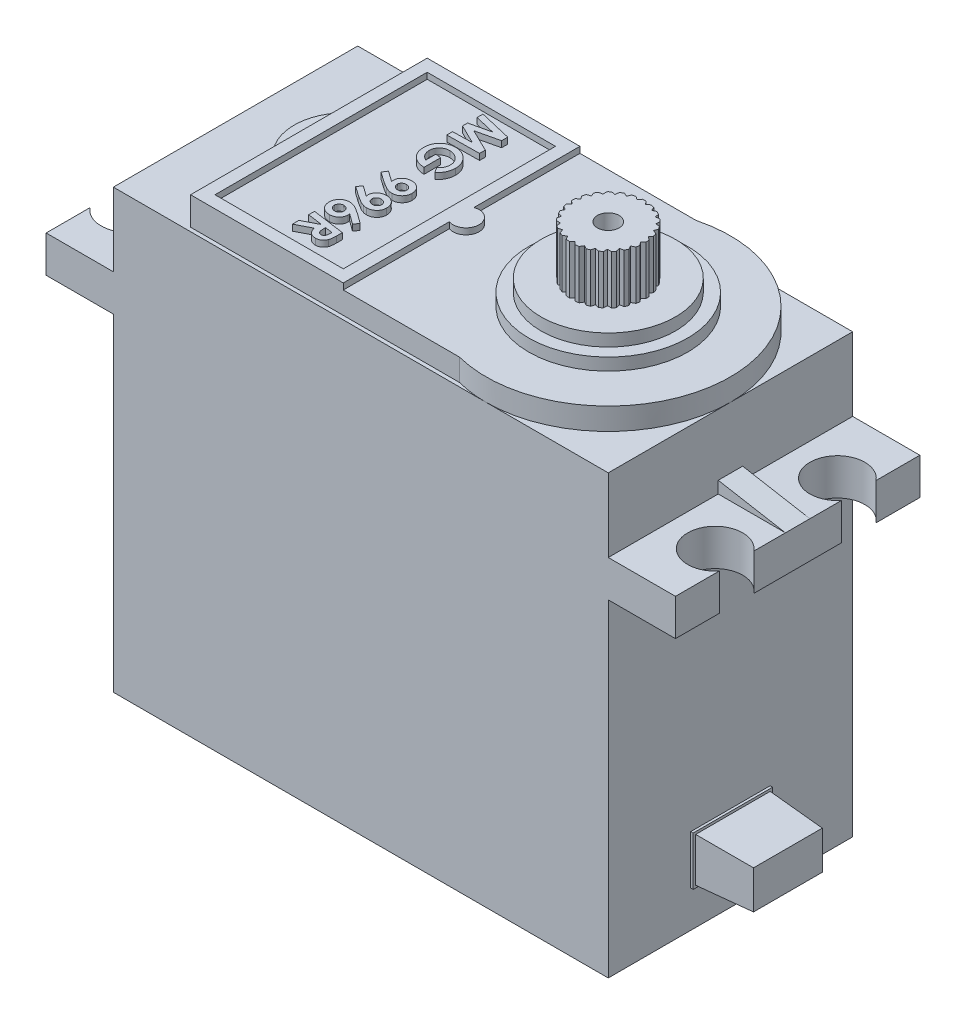
SolidWorks part; units mm, degrees
ref_plane "Plan de face" through (0, 0, 0) normal (0, 0, 1) x (1, 0, 0)
ref_plane "Plan de dessus" through (0, 0, 0) normal (0, 1, 0) x (1, 0, 0)
ref_plane "Plan de droite" through (0, 0, 0) normal (1, 0, 0) x (0, 0, -1)
sketch "Esquisse2" plane through (0, 0, 0) normal (0, 1, 0) x (1, 0, 0)
  line L1 (0, 0) -> (40.5, 0)
  line L2 (0, 0) -> (0, 20)
  line L3 (0, 20) -> (40.5, 20)
  line L4 (40.5, 0) -> (40.5, 20)
  dimension "D1" = 20
  dimension "D2" = 40.5
extrude "Boss.-Extru.1" add sketch "Esquisse2" along normal blind 36.8
chamfer "Chanfrein1" distance 1 angle 45 4 edges at (20.25, 0, 0) (40.5, 0, -10) (20.25, 0, -20) (0, 0, -10)
sketch "Esquisse3" plane through (40.5, 0, 0) normal (1, 0, 0) x (0, 0, -1)
  line L0 (19, 0) -> (1, 0) construction
  line L1 (6.75, 8) -> (13.25, 8)
  line L2 (6.75, 8) -> (6.75, 4)
  line L3 (6.75, 4) -> (13.25, 4)
  line L4 (13.25, 8) -> (13.25, 4)
  line L5 (10, 4) -> (10, 0) construction
  dimension "D1" = 4
  dimension "D2" = 4
  dimension "D3" = 6.5
extrude "Boss.-Extru.2" add sketch "Esquisse3" along normal blind 0.2
sketch "Esquisse4" plane through (40.7, 0, 0) normal (1, 0, 0) x (0, 0, -1)
  line L8 (6.95, 7.8) -> (6.95, 4.2)
  line L9 (6.95, 4.2) -> (13.05, 4.2)
  line L10 (13.05, 4.2) -> (13.05, 7.8)
  line L11 (13.05, 7.8) -> (6.95, 7.8)
  line L12 (6.95, 7.8) -> (6.95, 4.2)
  line L13 (6.95, 4.2) -> (13.05, 4.2)
  line L14 (13.05, 4.2) -> (13.05, 7.8)
  line L15 (13.05, 7.8) -> (6.95, 7.8)
  dimension "D1" = 0.2
extrude "Boss.-Extru.3" add sketch "Esquisse4" along normal blind 4.5 draft 3
ref_plane "Plan1" through (0, 30.8, 0) normal (0, 1, 0) x (1, 0, 0)
sketch "Esquisse5" plane through (0, 30.8, 0) normal (0, 1, 0) x (1, 0, 0)
  line L0 (40.5, 0) -> (40.5, 20) construction
  line L1 (40.5, 0) -> (46, 0)
  line L2 (40.5, 0) -> (40.5, 20)
  line L3 (40.5, 20) -> (46, 20)
  line L4 (46, 0) -> (46, 20)
  line L5 (40.5, 20) -> (0, 20) construction
  line L6 (0, 0) -> (40.5, 0) construction
  line L8 (0, 0) -> (-5.5, 0)
  line L9 (0, 0) -> (0, 20)
  line L10 (0, 20) -> (-5.5, 20)
  line L11 (-5.5, 0) -> (-5.5, 20)
  dimension "D1" = 5.5
extrude "Boss.-Extru.4" add sketch "Esquisse5" against normal blind 3
ref_plane "Plan2" through (0, 0, -10) normal (0, 0, -1) x (-1, 0, 0)
sketch "Esquisse7" plane through (0, 36.8, 0) normal (0, 1, 0) x (1, 0, 0)
  line L0 (0, 0) -> (40.5, 0) construction
  line L1 (40.5, 0) -> (40.5, 20) construction
  line L2 (40.5, 20) -> (0, 20) construction
  line L3 (6, 10) -> (0, 10) construction
  line L4 (28, 19.6825) -> (6, 19.6825)
  line L6 (28, 0.3175) -> (6, 0.3175)
  line L7 (6, 19.6825) -> (6, 12.9394)
  line L8 (0, 0) -> (0, 20) construction
  line L9 (6, 7.0606) -> (6, 0.3175)
  arc A0 (28, 0.3175) -> (28, 19.6825) centre (30.5, 10) ccw
  arc A1 (6, 12.9394) -> (6, 7.0606) centre (9, 10) ccw
  dimension "D4" = 4.2
  dimension "D1" = 6
  dimension "D3" = 24.5
  dimension "D5" = 21.5
  dimension "D6" = 3
ref_plane "Plan3" through (20.25, 0, 0) normal (-1, 0, 0) x (0, 0, 1)
extrude "Boss.-Extru.5" add sketch "Esquisse7" along normal blind 1.8
sketch "Esquisse8" plane through (0, 38.6, 0) normal (0, 1, 0) x (1, 0, 0)
  line L0 (6, 0.3175) -> (28, 0.3175) construction
  line L1 (6, 19.6825) -> (18.5, 19.6825)
  line L2 (6, 19.6825) -> (6, 0.3175)
  line L3 (6, 0.3175) -> (18.5, 0.3175)
  line L4 (18.5, 19.6825) -> (18.5, 0.3175)
  line L5 (7, 18.6825) -> (7, 1.3175)
  line L6 (7, 1.3175) -> (17.5, 1.3175)
  line L7 (17.5, 18.6825) -> (17.5, 1.3175)
  line L8 (7, 18.6825) -> (17.5, 18.6825)
  dimension "D1" = 12.5
  dimension "D2" = 1
extrude "Boss.-Extru.6" add sketch "Esquisse8" along normal blind 0.5
sketch "Esquisse6" plane through (0, 0, -10) normal (0, 0, -1) x (-1, 0, 0)
  line L0 (-46, 30.8) -> (-40.5, 31.7731)
  line L1 (-40.5, 36.8) -> (-40.5, 30.8) construction
rib "Nervure1" sketch "Esquisse6" sketch "Esquisse6" thickness 2 extrusion direction parallel to sketch draft on no parameters "D1"=2
mirror "Symétrie1" about plane through (20.25, 0, 0) normal (-1, 0, 0) of "Nervure1"
sketch "Esquisse9" plane through (0, 30.8, 0) normal (0, 1, 0) x (1, 0, 0)
  line L0 (-3.75, 15) -> (-3.75, 5) construction
  line L1 (-3.75, 5) -> (-3.75, 15) construction
  line L2 (-3.75, 15) -> (44.25, 15) construction
  line L3 (44.25, 15) -> (44.25, 5) construction
  line L4 (-3.75, 5) -> (44.25, 5) construction
  line L5 (20.25, 11) -> (20.25, -11) construction
  line L6 (-5.5, 10) -> (-3.75, 10) construction
  line L7 (-5.5, 11) -> (-5.5, 9) construction
  circle A0 centre (-3.75, 15) radius 2.25
  circle A1 centre (-3.75, 5) radius 2.25
  circle A2 centre (44.25, 15) radius 2.25
  circle A3 centre (44.25, 5) radius 2.25
  dimension "D1" = 4.5
  dimension "D2" = 10
  dimension "D3" = 48
  dimension "D4" = 24
extrude "Enlèv. mat.-Extru.1" cut sketch "Esquisse9" against normal blind 3
sketch "Esquisse10" plane through (0, 38.6, 0) normal (0, 1, 0) x (1, 0, 0)
  line L0 (17.5, 10) -> (18.864, 10) construction
  line L1 (17.5, 1.3175) -> (17.5, 18.6825) construction
  line L2 (12.25, 18.6825) -> (12.25, 1.3175) construction
  line L3 (17.5, 18.6825) -> (7, 18.6825) construction
  line L4 (7, 1.3175) -> (17.5, 1.3175) construction
  line L5 (12.25, 1.3175) -> (7, 1.3175) construction
  line L6 (7, 1.3175) -> (9.625, 1.3175) construction
  line L7 (9.625, 1.3175) -> (9.625, 18.6825) construction
  line L8 (17.5, 18.6825) -> (7, 18.6825) construction
  circle A0 centre (18.864, 10) radius 1.0694
  text T0 "<b><i>MG 996R</i></b>" font "Century Gothic" height in points 10
extrude "Boss.-Extru.7" add sketch "Esquisse10" along normal up to surface (0.5 mm away) up to face at (12.25, 39.1, -10)
sketch "Esquisse11" plane through (0, 38.6, 0) normal (0, 1, 0) x (1, 0, 0)
  circle A0 centre (30.5, 10) radius 6.5
  arc A1 (28, 0.3175) -> (28, 19.6825) centre (30.5, 10) ccw construction
  dimension "D1" = 13
extrude "Boss.-Extru.8" add sketch "Esquisse11" along normal blind 1
sketch "Esquisse12" plane through (0, 39.6, 0) normal (0, 1, 0) x (1, 0, 0)
  circle A0 centre (30.5, 10) radius 5.5
  circle A1 centre (30.5, 10) radius 6.5 construction
  dimension "D1" = 11
extrude "Boss.-Extru.9" add sketch "Esquisse12" along normal blind 1
sketch "Esquisse13" plane through (0, 40.6, 0) normal (0, 1, 0) x (1, 0, 0)
  circle A0 centre (30.5, 10) radius 3
  circle A1 centre (30.5, 10) radius 5.5 construction
  dimension "D1" = 6
extrude "Boss.-Extru.10" add sketch "Esquisse13" along normal blind 4
sketch "Esquisse14" plane through (0, 44.6, 0) normal (0, 1, 0) x (1, 0, 0)
  line L0 (30.3139, 7.0058) -> (30.5471, 7.239)
  line L1 (30.5471, 7.239) -> (30.7736, 7.0125)
  line L2 (29.859, 7.314) -> (30.0221, 7.0383)
  line L3 (29.5752, 7.1461) -> (29.859, 7.314)
  line L4 (29.2112, 7.5578) -> (29.3005, 7.2502)
  line L5 (28.8945, 7.4658) -> (29.2112, 7.5578)
  line L6 (28.6443, 7.955) -> (28.6544, 7.6349)
  line L7 (28.3147, 7.9447) -> (28.6443, 7.955)
  line L8 (28.1941, 8.4808) -> (28.1242, 8.1682)
  line L9 (27.8722, 8.5527) -> (28.1941, 8.4808)
  line L10 (27.8887, 9.102) -> (27.7433, 8.8166)
  line L11 (27.5948, 9.2517) -> (27.8887, 9.102)
  line L12 (27.7474, 9.7796) -> (27.5356, 9.5393)
  line L13 (27.5, 9.9977) -> (27.7474, 9.7796)
  line L14 (27.779, 10.4711) -> (27.5142, 10.291)
  line L15 (27.5937, 10.7438) -> (27.779, 10.4711)
  line L16 (27.9817, 11.1329) -> (27.6803, 11.0244)
  line L17 (27.87, 11.4432) -> (27.9817, 11.1329)
  line L18 (28.3425, 11.7236) -> (28.0237, 11.6935)
  line L19 (28.3115, 12.052) -> (28.3425, 11.7236)
  line L20 (28.839, 12.206) -> (28.5226, 12.2561)
  line L21 (28.8906, 12.5317) -> (28.839, 12.206)
  line L22 (29.4398, 12.5498) -> (29.1458, 12.677)
  line L23 (29.5707, 12.8525) -> (29.4398, 12.5498)
  line L24 (30.1072, 12.7333) -> (29.8541, 12.9296)
  line L25 (30.3093, 12.9939) -> (30.1072, 12.7333)
  line L26 (30.7993, 12.7452) -> (30.603, 12.9982)
  line L27 (31.0599, 12.9473) -> (30.7993, 12.7452)
  line L28 (31.4726, 12.5845) -> (31.3454, 12.8784)
  line L29 (31.7752, 12.7155) -> (31.4726, 12.5845)
  line L30 (32.0847, 12.2614) -> (32.0346, 12.5778)
  line L31 (32.4105, 12.313) -> (32.0847, 12.2614)
  line L32 (32.5974, 11.7963) -> (32.6275, 12.1151)
  line L33 (32.9257, 11.7652) -> (32.5974, 11.7963)
  line L34 (32.9782, 11.2182) -> (33.0867, 11.5196)
  line L35 (33.2885, 11.1065) -> (32.9782, 11.2182)
  line L36 (33.2033, 10.5637) -> (33.3833, 10.8286)
  line L37 (33.4761, 10.3783) -> (33.2033, 10.5637)
  line L38 (33.2585, 9.8737) -> (33.4988, 10.0855)
  line L39 (33.4766, 9.6263) -> (33.2585, 9.8737)
  line L40 (33.1405, 9.1916) -> (33.4258, 9.337)
  line L41 (33.2902, 8.8978) -> (33.1405, 9.1916)
  line L42 (32.8565, 8.5604) -> (33.169, 8.6302)
  line L43 (32.9284, 8.2385) -> (32.8565, 8.5604)
  line L44 (32.4244, 8.0196) -> (32.7445, 8.0095)
  line L45 (32.4141, 7.6899) -> (32.4244, 8.0196)
  line L46 (31.8714, 7.6032) -> (32.179, 7.5139)
  line L47 (31.7794, 7.2865) -> (31.8714, 7.6032)
  line L48 (31.2323, 7.3374) -> (31.508, 7.1744)
  line L49 (31.0644, 7.0536) -> (31.2323, 7.3374)
  line L50 (30.5, 10) -> (30.5471, 7.239) construction
  line L51 (30.5, 10) -> (29.859, 7.314) construction
  circle A0 centre (30.5, 10) radius 3 construction
  circle A3 centre (30.5, 10) radius 3
  circle A4 centre (30.5, 10) radius 3
  dimension "D2" = 14.4
  dimension "D3" = 0
  dimension "D1" = 25
extrude "Enlèv. mat.-Extru.2" cut sketch "Esquisse14" against normal blind 4 contours L9 L8 M4 | L7 L6 M4 | L5 L4 M4 | L3 L2 M4 | L1 L0 M4 | L49 L48 M4 | L47 L46 M4 | L45 L44 M4 | L43 L42 M4 | L11 L10 M4 | L13 L12 M4 | L15 L14 M4 | L17 L16 M4 | L21 L20 M4 | L19 L18 M4 | L23 L22 M4 | L25 L24 M4 | L27 L26 M4 | L29 L28 M4 | L31 L30 M4 | L33 L32 M4 | L35 L34 M4 | L37 L36 M4 | L39 L38 M4 | L41 L40 M4
hole_wizard "Trou taraudé #2-561" positions "Esquisse15" profile "Esquisse16" tap size "#2-56" standard "Ansi Inch"
sketch "Esquisse15" plane through (0, 44.6, 0) normal (0, 1, 0) x (1, 0, 0)
  point P0 (30.5, 10)
sketch "Esquisse16" plane through (30.5, 44.6, -10) normal (1, 0, 0) x (0, 0, 1)
  line L0 (0, 0) -> (0, 7.1742)
  line L1 (0, 7.1742) -> (0.889, 6.64)
  line L2 (0.889, 6.64) -> (0.889, 0)
  line L5 (0.889, 0) -> (0, 0)
  line L10 (0, 7.1742) -> (-0.889, 6.64) construction
  line L11 (0, -6.35) -> (0, 107.95) construction
  dimension "Diamètre du trou pour taraudage" = 1.778
  dimension "Profondeur du trou pour taraudage" = 6.64
  dimension "Angle de pointe" = 118
cosmetic thread "Filetage de perçage1"
sketch "Esquisse17" plane through (0, 0, 0) normal (0, -1, 0) x (1, 0, 0)
  line L0 (-357.3287, 115.5803) -> (-357.3287, 648.9137) construction
  line L1 (10.1301, -5.0147) -> (18.2112, -9.2602)
  line L2 (18.2112, -9.2602) -> (15.4455, -9.2602)
  line L3 (15.4455, -9.2602) -> (12.1334, -7.402)
  line L4 (12.1334, -7.402) -> (13.2682, -9.2602)
  line L5 (13.2682, -9.2602) -> (11.6452, -9.2602)
  line L6 (11.6452, -9.2602) -> (10.1301, -5.0147)
  line L7 (18.2112, -9.5408) -> (8.6259, -9.5408) construction
  line L8 (11.6452, -9.8214) -> (10.1301, -14.0669)
  line L9 (13.2682, -9.8214) -> (11.6452, -9.8214)
  line L10 (12.1334, -11.6797) -> (13.2682, -9.8214)
  line L11 (15.4455, -9.8214) -> (12.1334, -11.6797)
  line L12 (18.2112, -9.8214) -> (15.4455, -9.8214)
  line L13 (10.1301, -14.0669) -> (18.2112, -9.8214)
extrude "Enlèv. mat.-Extru.3" cut sketch "Esquisse17" against normal blind 0.5
